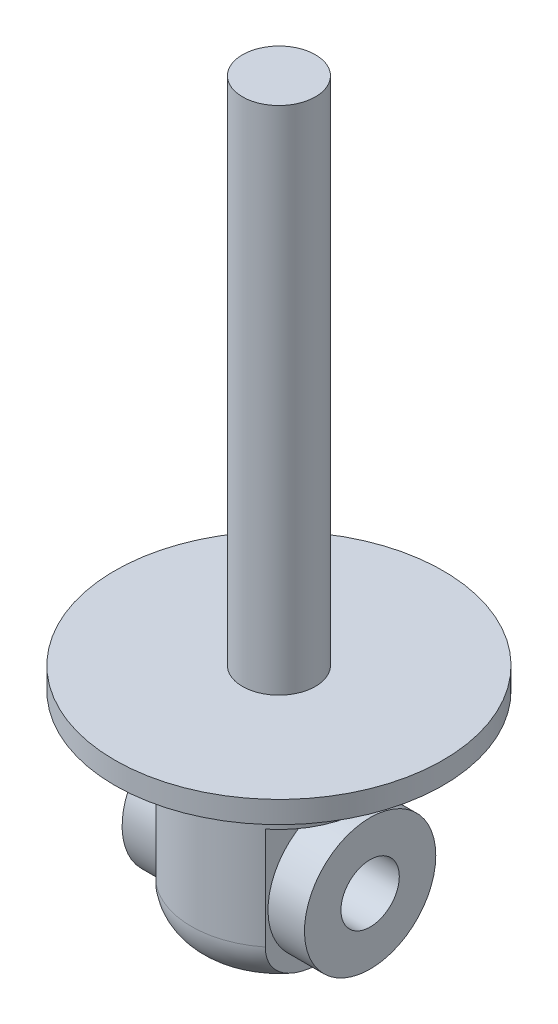
SolidWorks part; units mm, degrees
ref_plane "Front Plane" through (0, 0, 0) normal (0, 0, 1) x (1, 0, 0)
ref_plane "Top Plane" through (0, 0, 0) normal (0, 1, 0) x (1, 0, 0)
ref_plane "Right Plane" through (0, 0, 0) normal (1, 0, 0) x (0, 0, -1)
sketch "Sketch1" plane through (0, 0, 0) normal (0, 1, 0) x (1, 0, 0)
  circle A0 centre (0, 0) radius 22.5
  dimension "D1" = 45
extrude "Boss-Extrude1" add sketch "Sketch1" along normal blind 3
sketch "Sketch2" plane through (0, 3, 0) normal (0, 1, 0) x (1, 0, 0)
  circle A0 centre (0, 0) radius 5
extrude "Boss-Extrude2" add sketch "Sketch2" along normal blind 70
sketch "Sketch3" plane through (0, 0, 0) normal (0, -1, 0) x (1, 0, 0)
  circle A0 centre (0, 0) radius 12
  dimension "D1" = 24
extrude "Boss-Extrude3" add sketch "Sketch3" along normal blind 28
fillet "Fillet1" radius 6 1 edges at (0, -28, -12)
sketch "Sketch4" plane through (0, 0, 0) normal (0, 0, 1) x (1, 0, 0)
  line L0 (0, 0) -> (0, -52.2087) construction
  line L1 (0, -28) -> (60.7437, -28)
  line L2 (-6, -28) -> (6, -28) construction
  line L3 (60.7437, -28) -> (-62.3565, -28)
  line L4 (7.5, -28) -> (7.5, -8)
  line L5 (7.5, -8) -> (29.3652, -8)
  line L6 (29.3652, -8) -> (29.3652, -28)
  line L7 (29.3652, -28) -> (7.5, -28)
  line L8 (-29.3652, -28) -> (-7.5, -28)
  line L9 (-29.3652, -8) -> (-29.3652, -28)
  line L10 (-7.5, -8) -> (-29.3652, -8)
  line L11 (-7.5, -28) -> (-7.5, -8)
extrude "Cut-Extrude1" cut sketch "Sketch4" against normal through all both and the other way through all contours L6 L5 L4 L3 | L3 L11 L10 L9
sketch "Sketch5" plane through (7.5, 0, 0) normal (1, 0, 0) x (0, 0, -1)
  line L0 (0, -5.4037) -> (0, -32.6716) construction
  circle A0 centre (0, -17.8095) radius 4
  spline S0 degree 3 poles (9.3675, -22) (9.3675, -22.256) (9.346, -22.5161) (9.2617, -23.0236) (9.1993, -23.2718) (9.0353, -23.7573) (8.9325, -23.9966) (8.6933, -24.4529) (8.5573, -24.67) (8.2544, -25.0836) (8.0864, -25.2813) (7.7261, -25.6506) (7.5349, -25.8216) (6.9312, -26.2977) (6.4844, -26.5672) (5.5607, -27.0045) (5.0803, -27.1758) (4.0917, -27.4469) (3.5846, -27.5457) (2.5722, -27.6899) (2.0636, -27.7363) (1.0432, -27.7958) (0.5315, -27.8091) (-0.4943, -27.8098) (-1.0101, -27.797) (-2.0342, -27.7387) (-2.5445, -27.6929) (-3.56, -27.5501) (-4.0672, -27.4524) (-5.0646, -27.1812) (-5.5488, -27.0094) (-6.4792, -26.5703) (-6.9277, -26.3001) (-7.5323, -25.8239) (-7.7237, -25.6529) (-8.0841, -25.2839) (-8.2538, -25.0844) (-8.7096, -24.462) (-8.9491, -24.0109) (-9.1993, -23.2725) (-9.2623, -23.0206) (-9.3462, -22.5143) (-9.3675, -22.2585) (-9.3675, -22) knots 0 0 0 0 0.03125 0.03125 0.0625 0.0625 0.09375 0.09375 0.125 0.125 0.15625 0.15625 0.1875 0.1875 0.25 0.25 0.3125 0.3125 0.375 0.375 0.4375 0.4375 0.5 0.5 0.5625 0.5625 0.625 0.625 0.6875 0.6875 0.75 0.75 0.8125 0.8125 0.84375 0.84375 0.875 0.875 0.9375 0.9375 0.96875 0.96875 1 1 1 1 construction
  point P8 (0, -27.8095)
extrude "Cut-Extrude3" cut sketch "Sketch5" against normal through all both and the other way through all
sketch "Sketch7" plane through (0, 0, 0) normal (1, 0, 0) x (0, 0, -1)
  circle A0 centre (0, -17.8095) radius 9
  circle A1 centre (0, -17.8095) radius 4 construction
  circle A2 centre (0, -17.8095) radius 4
extrude "Boss-Extrude4" add sketch "Sketch7" along normal mid plane 25
